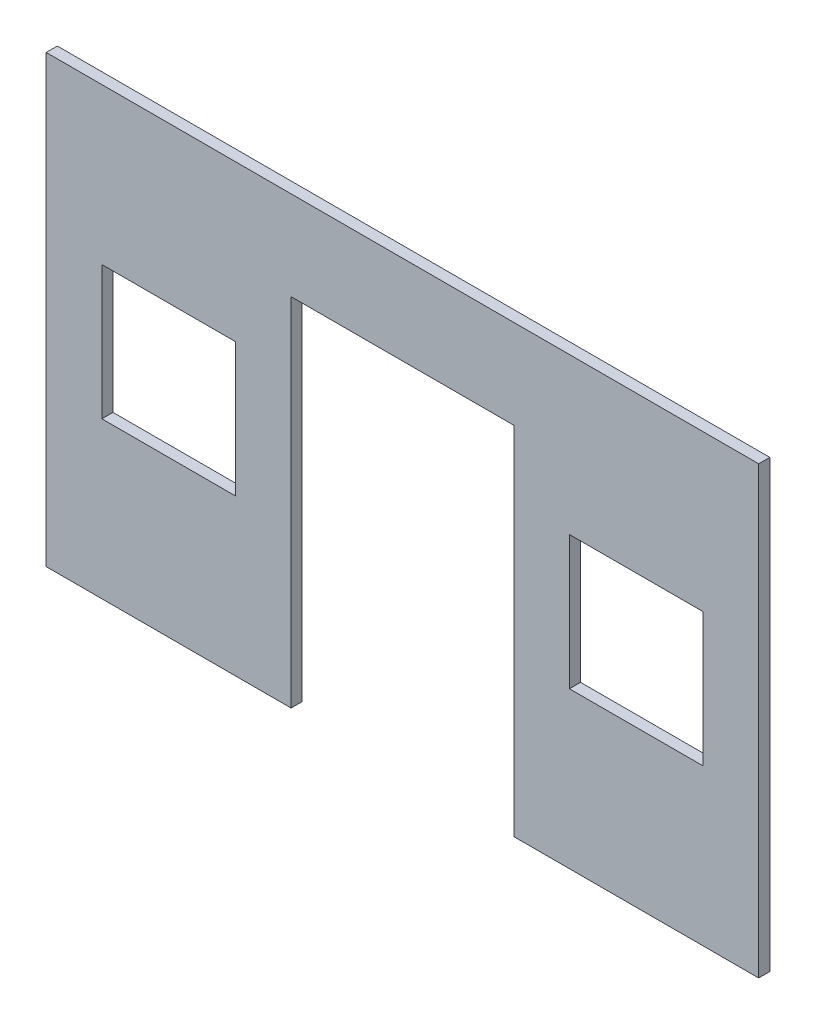
SolidWorks part; units mm, degrees
material "Oak"
ref_plane "Front" through (0, 0, 0) normal (0, 0, 1) x (1, 0, 0)
ref_plane "Top" through (0, 0, 0) normal (0, 1, 0) x (1, 0, 0)
ref_plane "Right" through (0, 0, 0) normal (1, 0, 0) x (0, 0, -1)
sketch "Sketch1" plane through (0, 0, 0) normal (0, 0, 1) x (1, 0, 0)
  line L1 (-203.2, 254) -> (203.2, 254)
  line L2 (-203.2, 254) -> (-203.2, 0)
  line L3 (-203.2, 0) -> (203.2, 0)
  line L4 (203.2, 254) -> (203.2, 0)
  point P4 (0, 0)
  dimension "D1" = 406.4
  dimension "D2" = 254
extrude "Boss-Extrude1" add sketch "Sketch1" along normal blind 6.35
sketch "Sketch2" plane through (0, 0, 6.35) normal (0, 0, 1) x (1, 0, 0)
  line L0 (-203.2, 0) -> (203.2, 0) construction
  line L1 (-63.5, 203.2) -> (63.5, 203.2)
  line L2 (-63.5, 203.2) -> (-63.5, 0)
  line L3 (-63.5, 0) -> (63.5, 0)
  line L4 (63.5, 203.2) -> (63.5, 0)
  point P6 (0, 203.2)
  dimension "D1" = 127
  dimension "D2" = 203.2
extrude "Cut-Extrude1" cut sketch "Sketch2" against normal up to next
sketch "Sketch3" plane through (0, 0, 6.35) normal (0, 0, 1) x (1, 0, 0)
  line L1 (-171.45, 165.1) -> (-95.25, 165.1)
  line L2 (-171.45, 165.1) -> (-171.45, 88.9)
  line L3 (-171.45, 88.9) -> (-95.25, 88.9)
  line L4 (-95.25, 165.1) -> (-95.25, 88.9)
  line L5 (-203.2, 0) -> (-63.5, 0) construction
  line L7 (203.2, 254) -> (-203.2, 254) construction
  point P4 (-133.35, 165.1)
  point P5 (-171.45, 127)
  point P9 (-133.35, 0)
  dimension "D1" = 76.2
  dimension "D2" = 76.2
  dimension "D3" = 127
extrude "Cut-Extrude3" cut sketch "Sketch3" against normal up to next
sketch "Sketch4" plane through (0, 0, 6.35) normal (0, 0, 1) x (1, 0, 0)
  line L0 (63.5, 0) -> (203.2, 0) construction
  line L1 (95.25, 165.1) -> (171.45, 165.1)
  line L2 (95.25, 165.1) -> (95.25, 88.9)
  line L3 (95.25, 88.9) -> (171.45, 88.9)
  line L4 (171.45, 165.1) -> (171.45, 88.9)
  line L5 (203.2, 254) -> (-203.2, 254) construction
  point P4 (133.35, 165.1)
  point P7 (133.35, 0)
  point P8 (171.45, 127)
  dimension "D1" = 76.2
  dimension "D2" = 76.2
  dimension "D3" = 127
extrude "Cut-Extrude4" cut sketch "Sketch4" against normal up to next
